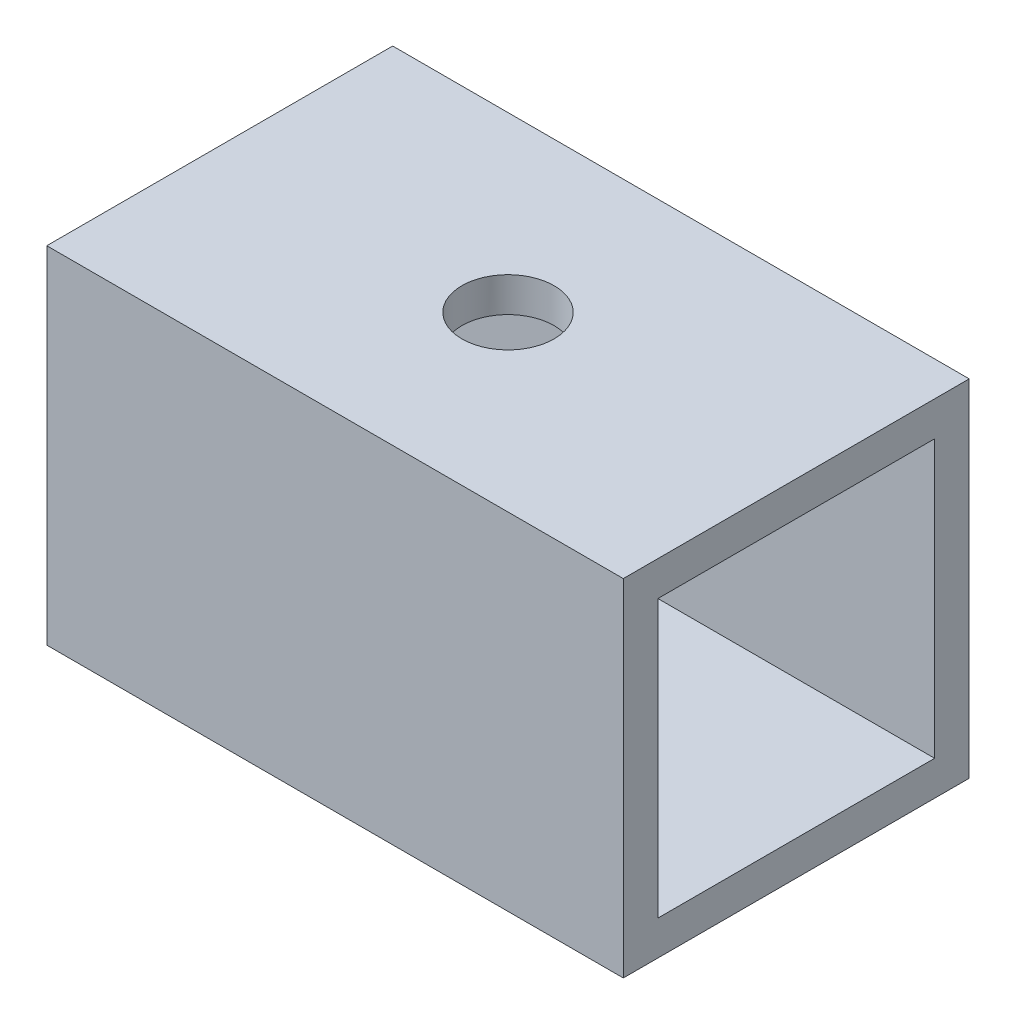
SolidWorks part; units mm, degrees
ref_plane "Front Plane" through (0, 0, 0) normal (0, 0, 1) x (1, 0, 0)
ref_plane "Top Plane" through (0, 0, 0) normal (0, 1, 0) x (1, 0, 0)
ref_plane "Right Plane" through (0, 0, 0) normal (1, 0, 0) x (0, 0, -1)
sketch "Sketch1" plane through (0, 0, 0) normal (1, 0, 0) x (0, 0, -1)
  line L0 (-6, 6) -> (6, 6)
  line L1 (-7.5, 7.5) -> (7.5, 7.5)
  line L2 (-7.5, 7.5) -> (-7.5, -7.5)
  line L3 (-7.5, -7.5) -> (7.5, -7.5)
  line L4 (7.5, 7.5) -> (7.5, -7.5)
  line L5 (-7.5, 7.5) -> (7.5, -7.5) construction
  line L6 (-7.5, -7.5) -> (7.5, 7.5) construction
  line L7 (6, 6) -> (6, -6)
  line L8 (-6, -6) -> (6, -6)
  line L9 (-6, 6) -> (-6, -6)
  point P0 (0, 0)
  dimension "D1" = 15
  dimension "D2" = 15
  dimension "D3" = 1.5
extrude "Boss-Extrude1" add sketch "Sketch1" along normal blind 25
sketch "Sketch2" plane through (0, 7.5, 0) normal (0, 1, 0) x (1, 0, 0)
  line L0 (0, 0) -> (25, 0) construction
  line L1 (25, 7.5) -> (25, -7.5) construction
  circle A0 centre (12.5, 0) radius 2
  dimension "D1" = 4
extrude "Cut-Extrude1" cut sketch "Sketch2" against normal through all
